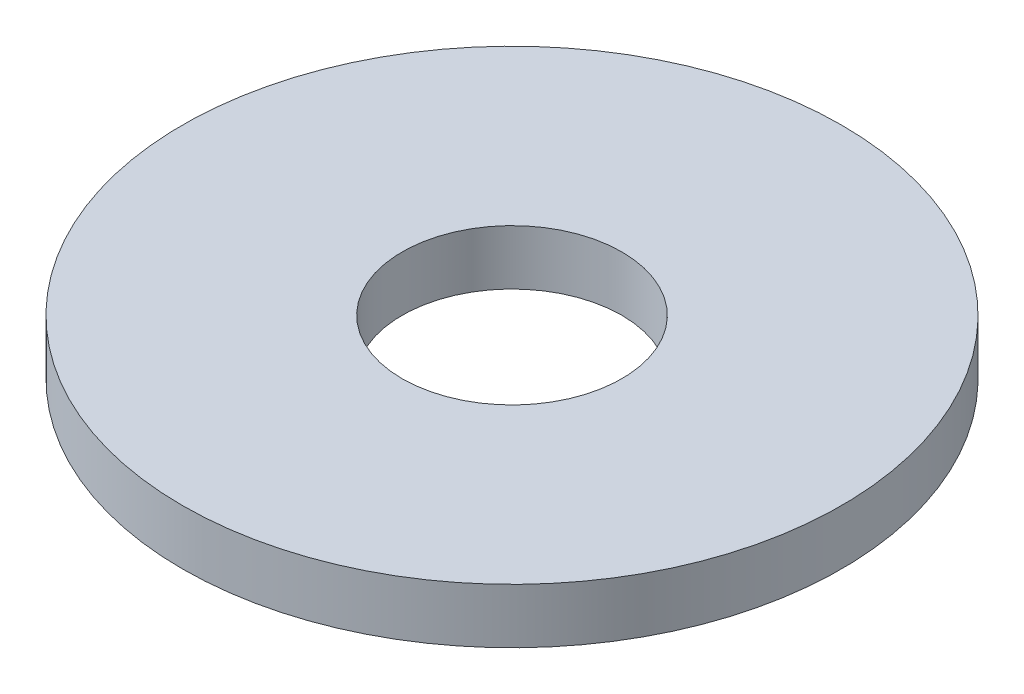
SolidWorks part; units mm, degrees
ref_plane "Спереди" through (0, 0, 0) normal (0, 0, 1) x (1, 0, 0)
ref_plane "Сверху" through (0, 0, 0) normal (0, 1, 0) x (1, 0, 0)
ref_plane "Справа" through (0, 0, 0) normal (1, 0, 0) x (0, 0, -1)
sketch "Эскиз1" plane through (0, 0, 0) normal (0, 1, 0) x (1, 0, 0)
  circle A0 centre (0, 0) radius 6
  circle A1 centre (0, 0) radius 2
extrude "Бобышка-Вытянуть1" add sketch "Эскиз1" along normal blind 1
